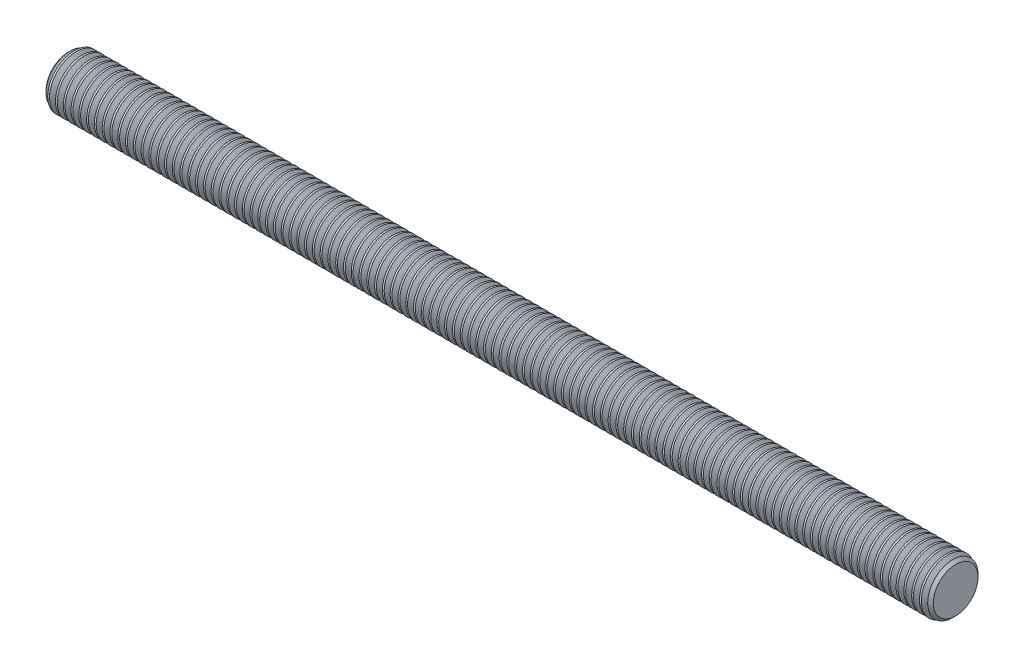
SolidWorks part; units mm, degrees
revolve "BaseBody" add sketch "BodySke" angle 360 about L14
sketch "BodySke" plane through (0, 0, 0) normal (0, 0, 1) x (1, 0, 0)
  line L0 (189.928, 15.875) -> (189.928, -6.35) construction
  line L1 (1.75, 15.875) -> (1.75, -3.175) construction
  line L2 (200, 6.35) -> (200, 3.175) construction
  line L10 (0, 6) -> (200, 6)
  line L12 (200, 6) -> (200, 0)
  line L13 (200, 0) -> (0, 0)
  line L14 (-3.175, 0) -> (107.95, 0) construction
  line L18 (0, 6) -> (0, 0)
  dimension "Diameter" = 12
  dimension "Length" = 200
  dimension "Advance" = 1.75
  dimension "Minor_dia" = 10.072
  dimension "Thread_max" = 200
cosmetic thread "ThreadCosmetic" [suppressed] parameters "Thread_minor"=10.072
material "AISI 304"
ref_plane "Plane1" through (0, 0, 0) normal (0, 0, 1) x (1, 0, 0)
ref_plane "Plane2" through (0, 0, 0) normal (0, 1, 0) x (1, 0, 0)
ref_plane "Plane3" through (0, 0, 0) normal (1, 0, 0) x (0, 0, -1)
other "Configuration Table"
chamfer "Chamfer1" distance 0.964 angle 45 2 edges at (200, 0, 6) (0, 0, 6)
sketch "ThdSchSke" plane through (0, 0, 0) normal (0, 0, 1) x (1, 0, 0)
  line L0 (0.675, -5.036) -> (0, -6)
  line L1 (0.675, -5.036) -> (1.35, -6)
  line L2 (1.35, -6) -> (1.35, -7.5)
  line L3 (-3.175, 0) -> (5.1513, 0) construction
  line L4 (0, 6) -> (0, -6) construction
  line L5 (1.35, -7.5) -> (0, -7.5)
  line L6 (0, -7.5) -> (0, -6)
  dimension "Thread_minor" = 10.072
  dimension "Diameter" = 12
revolve "ThreadSchematic" cut sketch "ThdSchSke" angle 360 about L3
pattern_linear "ThdSchPat" count 114 spacing 1.7544 along (1, 0, 0) of "ThreadSchematic"
equation "\"Thread_minor@ThreadCosmetic\" = \"Minor_dia@BodySke\""
equation "\"Chamfer@Chamfer1\" =  ( \"Diameter@BodySke\" - \"Minor_dia@BodySke\" ) / 2"
equation "\"Thread_minor@ThdSchSke\" = \"Minor_dia@BodySke\""
equation "\"Diameter@ThdSchSke\" = \"Diameter@BodySke\""
equation "\"Overcut@ThdSchSke\" = \"Diameter@BodySke\" * 1.25"
equation "\"Num_threads@ThdSchPat\" = int( (\"Thread_max@BodySke\" - \"Advance@BodySke\" ) / \"Advance@BodySke\" + 0.999 ) + 1"
equation "\"Advance@ThdSchPat\" = \"Thread_max@BodySke\" /  ( \"Num_threads@ThdSchPat\" - 1 ) 'relax it"
equation "\"Num_threads@ThdSchPat\" = \"Num_threads@ThdSchPat\" - sgn( \"Num_threads@ThdSchPat\" - 1 ) '---chamfered tips only---"
